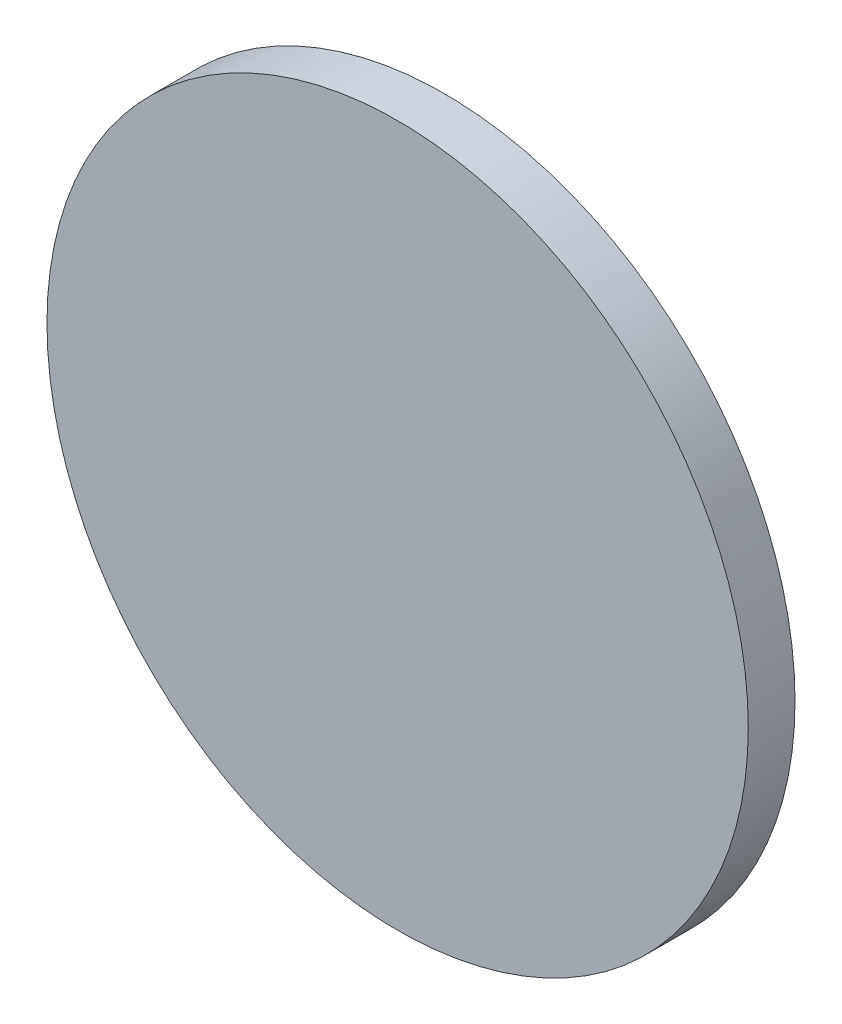
SolidWorks part; units mm, degrees
material "Rubber"
ref_plane "Front Plane" through (0, 0, 0) normal (0, 0, 1) x (1, 0, 0)
ref_plane "Top Plane" through (0, 0, 0) normal (0, 1, 0) x (1, 0, 0)
ref_plane "Right Plane" through (0, 0, 0) normal (1, 0, 0) x (0, 0, -1)
sketch "Sketch1" plane through (0, 0, 0) normal (0, 0, 1) x (1, 0, 0)
  line L0 (500, -250) -> (450, -300) construction
  circle A0 centre (475, -275) radius 15
  dimension "D1" = 30
extrude "Boss-Extrude1" add sketch "Sketch1" along normal blind 2
